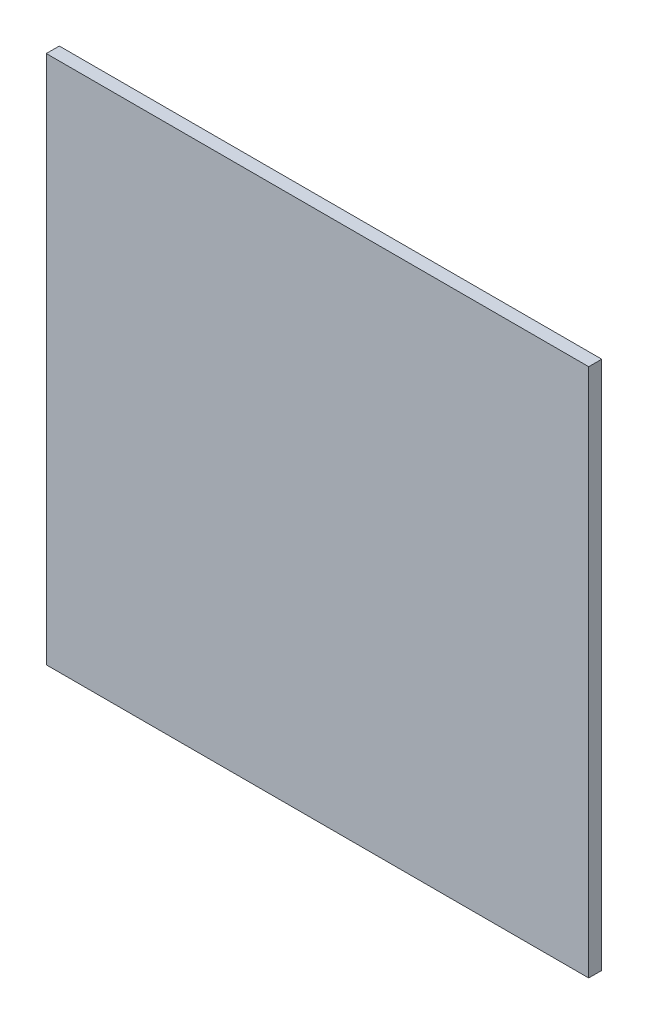
SolidWorks part; units mm, degrees
material "ASTM A36 Steel"
ref_plane "Front Plane" through (0, 0, 0) normal (0, 0, 1) x (1, 0, 0)
ref_plane "Top Plane" through (0, 0, 0) normal (0, 1, 0) x (1, 0, 0)
ref_plane "Right Plane" through (0, 0, 0) normal (1, 0, 0) x (0, 0, -1)
sketch "Sketch1" plane through (0, 0, 0) normal (0, 0, 1) x (1, 0, 0)
  line L1 (99.2187, 96.8375) -> (-99.2188, 96.8375)
  line L2 (99.2187, 96.8375) -> (99.2187, -96.8375)
  line L3 (99.2187, -96.8375) -> (-99.2188, -96.8375)
  line L4 (-99.2188, 96.8375) -> (-99.2188, -96.8375)
  line L5 (99.2187, 96.8375) -> (-99.2188, -96.8375) construction
  line L6 (99.2187, -96.8375) -> (-99.2188, 96.8375) construction
  point P0 (0, 0)
  dimension "D1" = 193.675
  dimension "D2" = 198.4375
extrude "Boss-Extrude1" add sketch "Sketch1" along normal blind 4.7625
